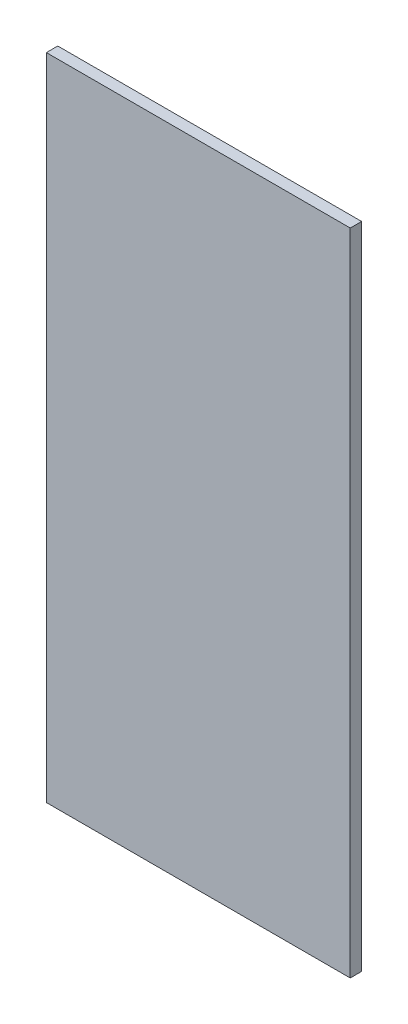
SolidWorks part; units mm, degrees
ref_plane "Plano frontal" through (0, 0, 0) normal (0, 0, 1) x (1, 0, 0)
ref_plane "Plano superior" through (0, 0, 0) normal (0, 1, 0) x (1, 0, 0)
ref_plane "Plano direito" through (0, 0, 0) normal (1, 0, 0) x (0, 0, -1)
sketch "Esboço1" plane through (0, 0, 0) normal (0, 0, 1) x (1, 0, 0)
  line L1 (-33.3721, 26.7442) -> (46.6279, 26.7442)
  line L2 (-33.3721, 26.7442) -> (-33.3721, -144.2558)
  line L3 (-33.3721, -144.2558) -> (46.6279, -144.2558)
  line L4 (46.6279, 26.7442) -> (46.6279, -144.2558)
  dimension "D1" = 80
  dimension "D2" = 171
extrude "Ressalto-extrusão1" add sketch "Esboço1" along normal blind 3
